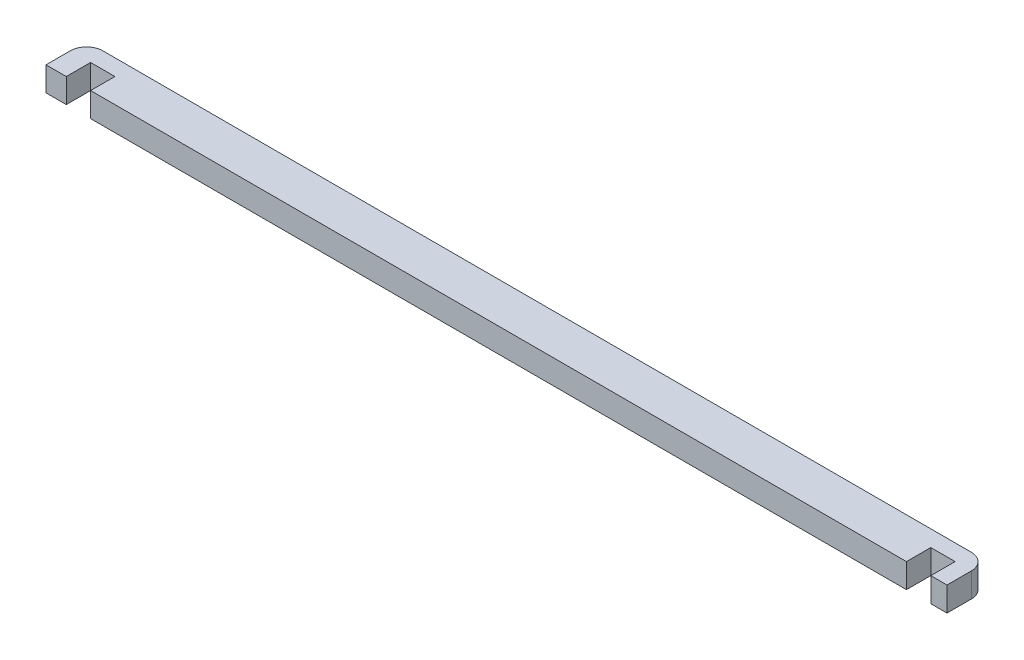
SolidWorks part; units mm, degrees
ref_plane "Alzado" through (0, 0, 0) normal (0, 0, 1) x (1, 0, 0)
ref_plane "Planta" through (0, 0, 0) normal (0, 1, 0) x (1, 0, 0)
ref_plane "Vista lateral" through (0, 0, 0) normal (1, 0, 0) x (0, 0, -1)
sketch "Croquis1" plane through (0, 0, 0) normal (0, 1, 0) x (1, 0, 0)
  line L0 (55.55, 5) -> (55.55, 0) construction
  line L1 (0, 0) -> (2.5, 0)
  line L2 (0, 0) -> (0, 5)
  line L3 (0, 5) -> (111.1, 5)
  line L4 (111.1, 0) -> (111.1, 5)
  line L6 (2.5, 0) -> (2.5, 3)
  line L7 (2.5, 3) -> (5.5, 3)
  line L8 (5.5, 0) -> (5.5, 3)
  line L10 (106.1, 0) -> (106.1, 3)
  line L11 (106.1, 3) -> (109.1, 3)
  line L12 (109.1, 0) -> (109.1, 3)
  line L13 (5.5, 0) -> (106.1, 0)
  line L14 (109.1, 0) -> (111.1, 0)
  dimension "D7" = 106.6
  dimension "D1" = 5
  dimension "D2" = 2
  dimension "D3" = 3
  dimension "D4" = 3
  dimension "D5" = 3
  dimension "D6" = 3
  dimension "D8" = 2.5
extrude "Saliente-Extruir1" add sketch "Croquis1" along normal blind 3
fillet "Redondeo1" radius 2 2 edges at (0, 1.5, -5) (111.1, 1.5, -5)
